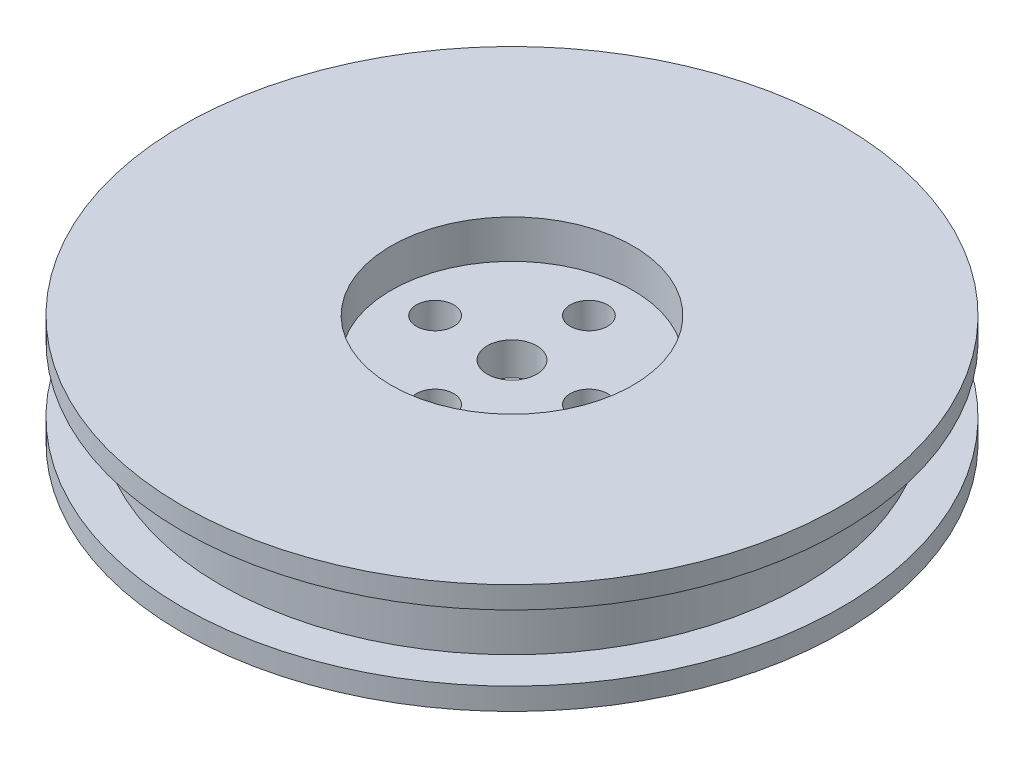
SolidWorks part; units mm, degrees
ref_plane "Front Plane" through (0, 0, 0) normal (0, 0, 1) x (1, 0, 0)
ref_plane "Top Plane" through (0, 0, 0) normal (0, 1, 0) x (1, 0, 0)
ref_plane "Right Plane" through (0, 0, 0) normal (1, 0, 0) x (0, 0, -1)
sketch "Sketch1" plane through (0, 0, 0) normal (0, 1, 0) x (1, 0, 0)
  circle A0 centre (0, 0) radius 30
extrude "c" add sketch "Sketch1" along normal blind 2
sketch "Sketch2" plane through (0, 2, 0) normal (0, 1, 0) x (1, 0, 0)
  circle A0 centre (0, 0) radius 26.5
extrude "Boss-Extrude2" add sketch "Sketch2" along normal blind 6
sketch "Sketch3" plane through (0, 8, 0) normal (0, 1, 0) x (1, 0, 0)
  circle A0 centre (0, 0) radius 30
extrude "Boss-Extrude3" add sketch "Sketch3" along normal blind 2
sketch "Sketch8" plane through (0, 0, 0) normal (0, -1, 0) x (1, 0, 0)
  circle A0 centre (0, 0) radius 11
  dimension "D1" = 22
extrude "Cut-Extrude2" cut sketch "Sketch8" against normal blind 3.5
sketch "Sketch9" plane through (0, 10, 0) normal (0, 1, 0) x (1, 0, 0)
  circle A0 centre (0, 0) radius 11
  dimension "D1" = 22
extrude "Cut-Extrude3" cut sketch "Sketch9" against normal blind 3.5
sketch "Sketch10" plane through (0, 6.5, 0) normal (0, 1, 0) x (1, 0, 0)
  circle A0 centre (0, 0) radius 2.25
extrude "Cut-Extrude4" cut sketch "Sketch10" against normal blind 12.5
sketch "Sketch12" plane through (0, 6.5, 0) normal (0, 1, 0) x (1, 0, 0)
  circle A0 centre (0, 7) radius 1.7
  circle A1 centre (7, 0) radius 1.7
  circle A2 centre (0, -7) radius 1.7
  circle A3 centre (-7, 0) radius 1.7
  point P12 (0, 0)
  dimension "D1" = 7
  dimension "D2" = 4
extrude "Cut-Extrude5" cut sketch "Sketch12" against normal blind 10
